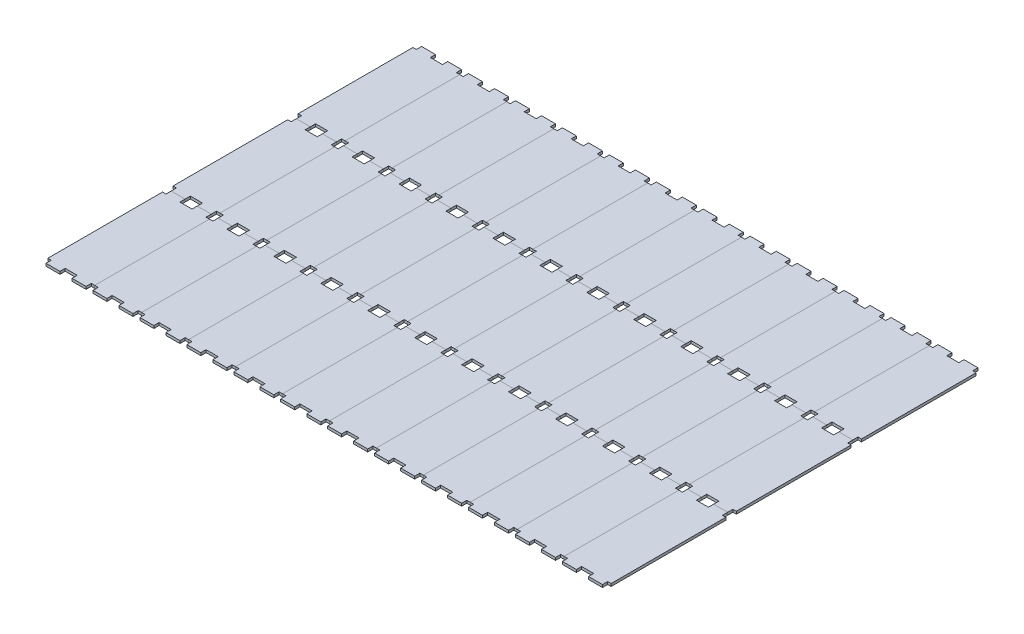
SolidWorks part; units mm, degrees
material "Cedar"
ref_plane "Front Plane" through (0, 0, 0) normal (0, 0, 1) x (1, 0, 0)
ref_plane "Top Plane" through (0, 0, 0) normal (0, 1, 0) x (1, 0, 0)
ref_plane "Right Plane" through (0, 0, 0) normal (1, 0, 0) x (0, 0, -1)
sketch "Sketch1" plane through (0, 0, 0) normal (0, 1, 0) x (1, 0, 0)
  line L1 (-28.575, 76.2) -> (28.575, 76.2)
  line L2 (-28.575, 76.2) -> (-28.575, -76.2)
  line L3 (-28.575, -76.2) -> (28.575, -76.2)
  line L4 (28.575, 76.2) -> (28.575, -76.2)
  line L5 (-28.575, 76.2) -> (28.575, -76.2) construction
  line L6 (-28.575, -76.2) -> (28.575, 76.2) construction
  point P0 (0, 0)
  dimension "D1" = 57.15
  dimension "D2" = 152.4
extrude "Boss-Extrude1" add sketch "Sketch1" along normal blind 3.175
sketch "Sketch2" plane through (0, 3.175, 0) normal (0, 1, 0) x (1, 0, 0)
  line L0 (-28.575, -69.85) -> (28.575, -69.85) construction
  line L1 (-28.575, 76.2) -> (-28.575, -76.2) construction
  line L2 (28.575, -76.2) -> (28.575, 76.2) construction
  line L3 (0, -76.2) -> (0, -69.85) construction
  line L4 (-28.575, -76.2) -> (28.575, -76.2) construction
  line L5 (-24.38, -69.85) -> (-28.575, -69.85)
  line L6 (-24.38, -69.85) -> (-7.37, -69.85) construction
  line L7 (-24.38, -69.85) -> (-24.38, -76.2)
  line L8 (-24.38, -76.2) -> (-7.37, -76.2) construction
  line L9 (-7.37, -69.85) -> (-7.37, -76.2)
  line L10 (-24.38, -69.85) -> (-7.37, -76.2) construction
  line L11 (-24.38, -76.2) -> (-7.37, -69.85) construction
  line L12 (-28.575, -69.85) -> (-28.575, -76.2)
  line L13 (-28.575, -76.2) -> (-24.38, -76.2)
  line L14 (-7.37, -76.2) -> (7.37, -76.2)
  line L15 (0, -76.2) -> (0, -69.85)
  line L16 (7.37, -69.85) -> (-7.37, -69.85)
  line L17 (24.38, -76.2) -> (7.37, -69.85) construction
  line L18 (24.38, -69.85) -> (7.37, -76.2) construction
  line L19 (24.38, -76.2) -> (7.37, -76.2) construction
  line L20 (24.38, -69.85) -> (7.37, -69.85) construction
  line L21 (28.575, -76.2) -> (24.38, -76.2)
  line L22 (28.575, -69.85) -> (28.575, -76.2)
  line L23 (7.37, -69.85) -> (7.37, -76.2)
  line L24 (24.38, -69.85) -> (24.38, -76.2)
  line L25 (24.38, -69.85) -> (28.575, -69.85)
  point P10 (-15.875, -73.025)
  point P22 (15.875, -73.025)
  line M12 (28.575, -76.2) -> (28.575, 76.2)
  line M14 (-28.575, 76.2) -> (-28.575, -76.2)
  line M15 (-28.575, -76.2) -> (28.575, -76.2)
  dimension "D1" = 6.35
  dimension "D2" = 7.37
  dimension "D3" = 17.01
extrude "Cut-Extrude1" cut sketch "Sketch2" against normal through all contours L7 L5 M14 M15 | L15 L16 L9 M15 | L23 L16 L15 L14 | L25 L24 M15 M12
mirror "Mirror1" about plane through (0, 0, 0) normal (0, 0, 1) of "Cut-Extrude1"
pattern_linear "LPattern1" count 12 spacing 57.15 along (1, 0, 0) count 3 spacing 152.4 along (0, 0, 1) of bodies 103
